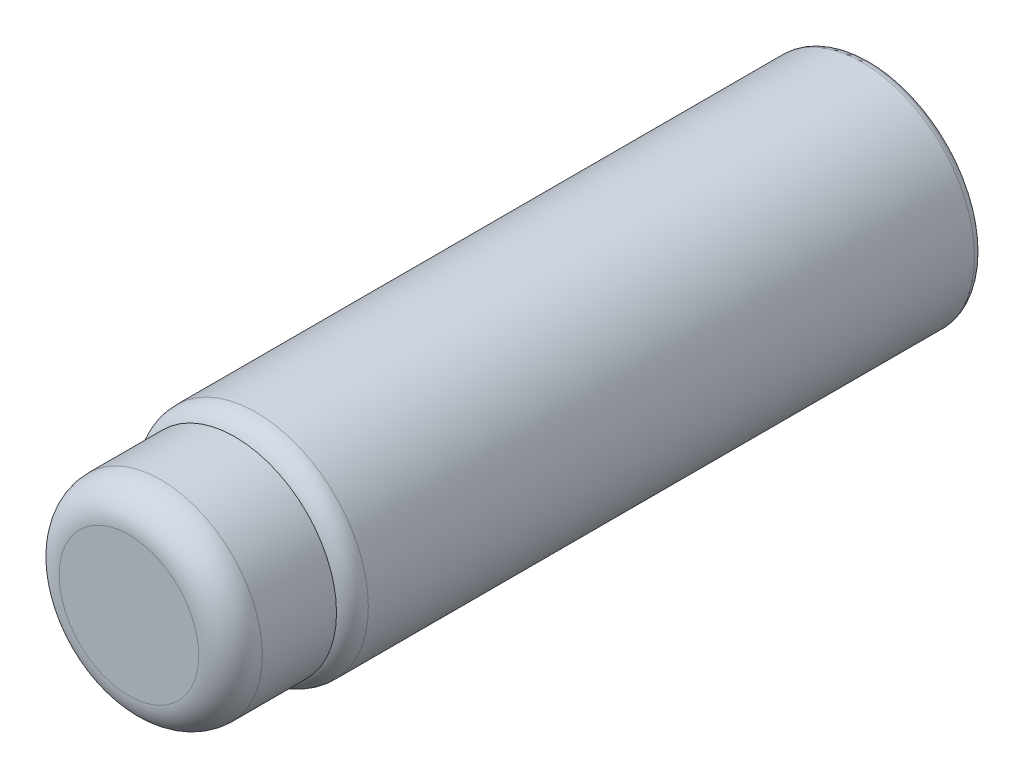
SolidWorks part; units mm, degrees
ref_plane "Front Plane" through (0, 0, 0) normal (0, 0, 1) x (1, 0, 0)
ref_plane "Top Plane" through (0, 0, 0) normal (0, 1, 0) x (1, 0, 0)
ref_plane "Right Plane" through (0, 0, 0) normal (1, 0, 0) x (0, 0, -1)
sketch "Sketch1" plane through (0, 0, 0) normal (0, 0, 1) x (1, 0, 0)
  circle A0 centre (0, 0) radius 52.9366
extrude "Boss-Extrude1" add sketch "Sketch1" along normal blind 300
fillet "Fillet1" radius 10 1 edges at (52.9366, 0, 300)
sketch "Sketch2" plane through (0, 0, 300) normal (0, 0, 1) x (1, 0, 0)
  circle A0 centre (0, 0) radius 47.9366
extrude "Boss-Extrude2" add sketch "Sketch2" along normal blind 50
fillet "Fillet2" radius 15 1 edges at (47.9366, 0, 350)
sketch "Sketch3" plane through (0, 0, 0) normal (0, 0, -1) x (-1, 0, 0)
  circle A0 centre (0, 0) radius 43.9227
extrude "Cut-Extrude1" cut sketch "Sketch3" against normal blind 10
fillet "Fillet3" radius 5 1 edges at (-43.9227, 0, 0)
fillet "Fillet4" radius 4 1 edges at (52.9366, 0, 0)
